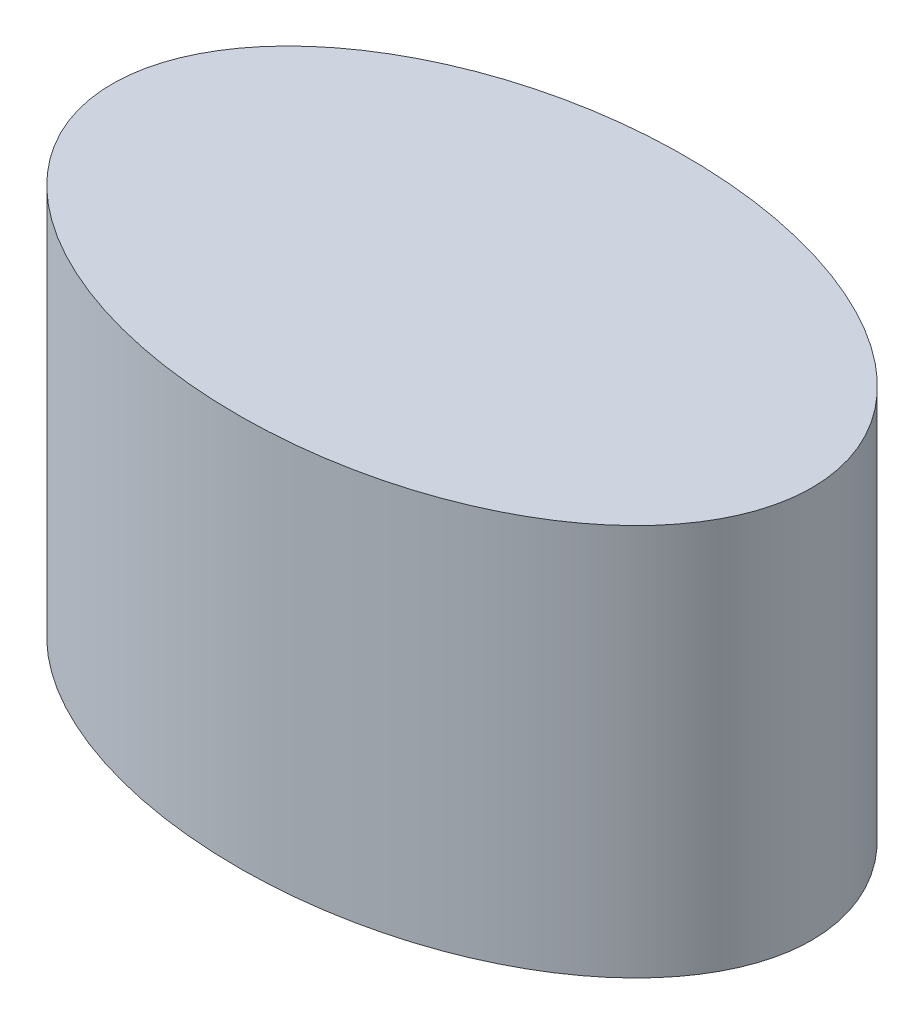
SolidWorks part; units mm, degrees
material "鎳"
ref_plane "前基準面" through (0, 0, 0) normal (0, 0, 1) x (1, 0, 0)
ref_plane "上基準面" through (0, 0, 0) normal (0, 1, 0) x (1, 0, 0)
ref_plane "右基準面" through (0, 0, 0) normal (1, 0, 0) x (0, 0, -1)
sketch "草圖1" plane through (0, 0, 0) normal (0, 1, 0) x (1, 0, 0)
  ellipse E0 centre (0, 0) end of major axis (25, 0) minor radius 16
  point P1 (0, 0)
  dimension "D1" = 50
  dimension "D2" = 32
extrude "填料-伸長1" add sketch "草圖1" along normal blind 28
sketch3d "URDF Reference"
  line L0 (0, 0, 0) -> (10, 0, 0) construction
  line L1 (0, 0, 0) -> (0, 0, -10) construction
  point P0 (0, 0, 0)
  point P1 (0, 0, 0)
